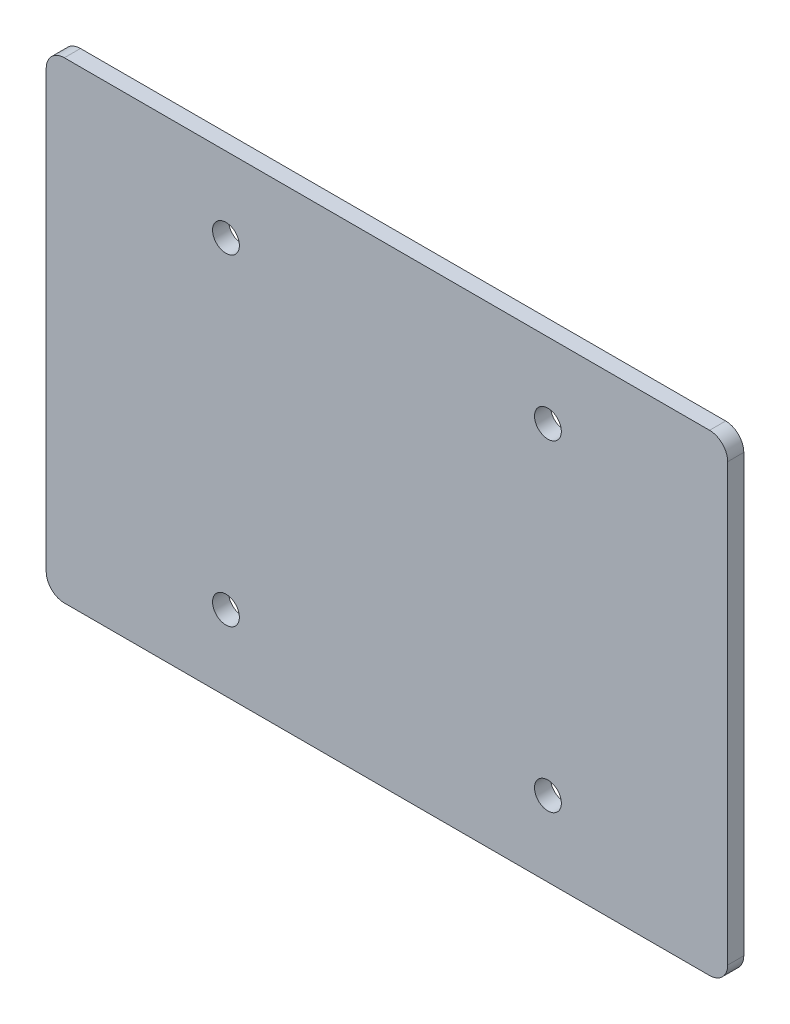
SolidWorks part; units mm, degrees
ref_plane "Front Plane" through (0, 0, 0) normal (0, 0, 1) x (1, 0, 0)
ref_plane "Top Plane" through (0, 0, 0) normal (0, 1, 0) x (1, 0, 0)
ref_plane "Right Plane" through (0, 0, 0) normal (1, 0, 0) x (0, 0, -1)
sketch "Sketch2" plane through (0, 0, 0) normal (0, 0, 1) x (1, 0, 0)
  line L1 (-63.5, -44) -> (63.5, -44)
  line L2 (-63.5, -44) -> (-63.5, 44)
  line L3 (-63.5, 44) -> (63.5, 44)
  line L4 (63.5, -44) -> (63.5, 44)
  line L5 (-63.5, -44) -> (63.5, 44) construction
  line L6 (-63.5, 44) -> (63.5, -44) construction
  point P0 (0, 0)
  dimension "D1" = 88
  dimension "D2" = 127
extrude "Boss-Extrude1" add sketch "Sketch2" along normal blind 3
fillet "Fillet1" radius 3.38 4 edges at (-63.5, -44, 1.5) (63.5, -44, 1.5) (63.5, 44, 1.5) (-63.5, 44, 1.5)
sketch "Sketch3" plane through (0, 0, 0) normal (0, 0, -1) x (-1, 0, 0)
  circle A0 centre (-30, -30) radius 2.5
  circle A1 centre (-30, 30) radius 2.5
  circle A2 centre (30, 30) radius 2.5
  circle A3 centre (30, -30) radius 2.5
extrude "Cut-Extrude1" cut sketch "Sketch3" against normal through all
